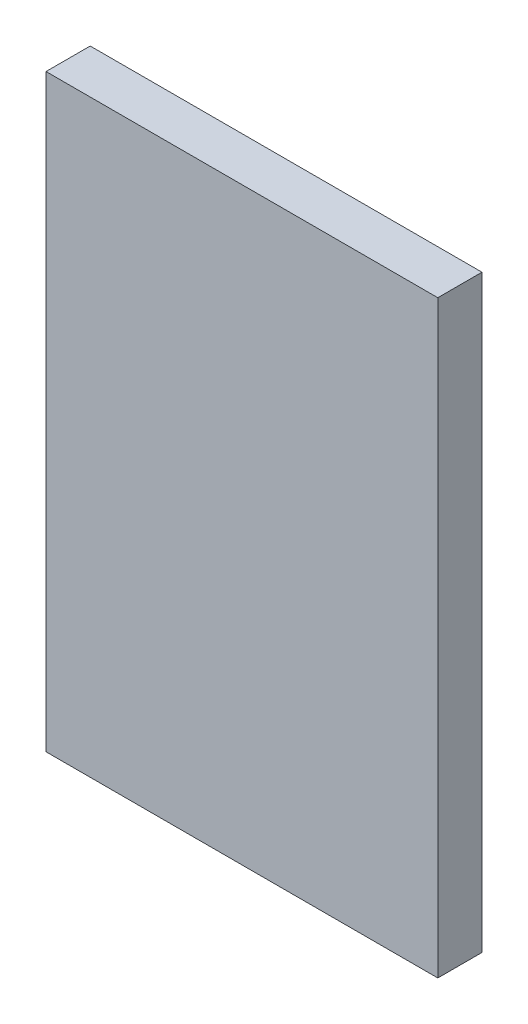
SolidWorks part; units mm, degrees
material "POLYURETHANE (11671)"
ref_plane "Front Plane" through (0, 0, 0) normal (0, 0, 1) x (1, 0, 0)
ref_plane "Top Plane" through (0, 0, 0) normal (0, 1, 0) x (1, 0, 0)
ref_plane "Right Plane" through (0, 0, 0) normal (1, 0, 0) x (0, 0, -1)
sketch "Sketch1" plane through (0, 0, 0) normal (0, 0, 1) x (1, 0, 0)
  line L1 (0, 0) -> (1330, 0)
  line L2 (0, 0) -> (0, -2000)
  line L3 (0, -2000) -> (1330, -2000)
  line L4 (1330, 0) -> (1330, -2000)
  dimension "D1" = 2000
  dimension "D2" = 1330
extrude "Boss-Extrude1" add sketch "Sketch1" along normal blind 150
